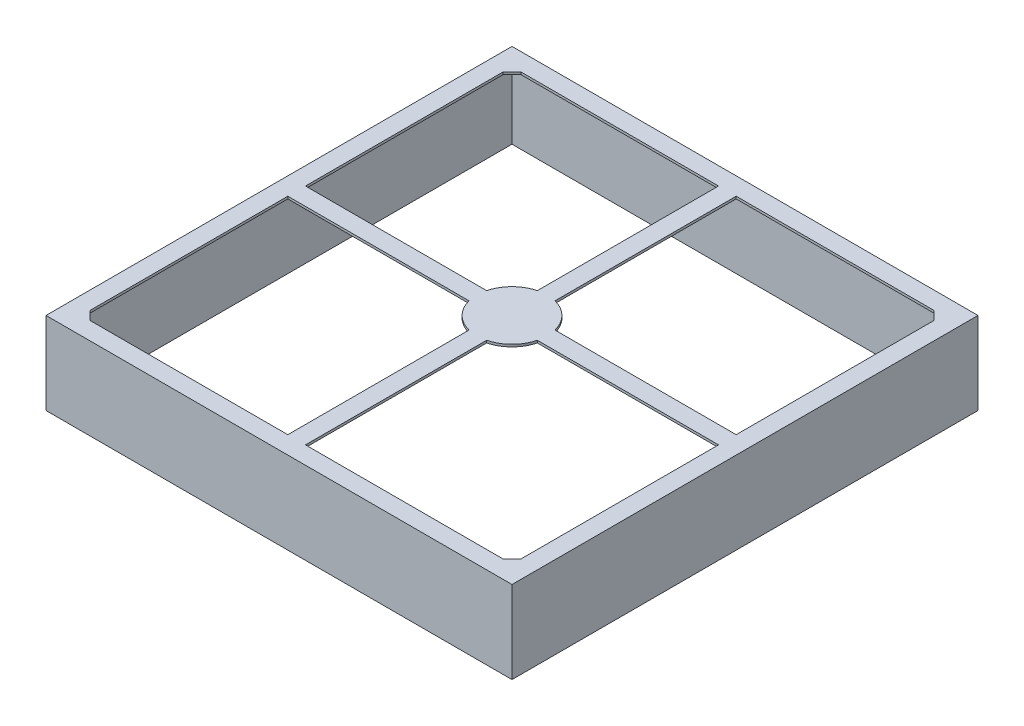
SolidWorks part; units mm, degrees
material "Magnesium Alloy"
ref_plane "Front Plane" through (0, 0, 0) normal (0, 0, 1) x (1, 0, 0)
ref_plane "Top Plane" through (0, 0, 0) normal (0, 1, 0) x (1, 0, 0)
ref_plane "Right Plane" through (0, 0, 0) normal (1, 0, 0) x (0, 0, -1)
sketch "Sketch1" plane through (0, 0, 0) normal (0, 1, 0) x (1, 0, 0)
  line L1 (-19.8, -19.8) -> (19.8, -19.8)
  line L2 (-19.8, -19.8) -> (-19.8, 19.8)
  line L3 (-19.8, 19.8) -> (19.8, 19.8)
  line L4 (19.8, -19.8) -> (19.8, 19.8)
  line L5 (-19.8, -19.8) -> (19.8, 19.8) construction
  line L6 (-19.8, 19.8) -> (19.8, -19.8) construction
  point P0 (0, 0)
  dimension "D1" = 39.6
extrude "Boss-Extrude1" add sketch "Sketch1" along normal blind 7
shell "Shell2" thickness 0.2
sketch "Sketch2" plane through (0, 0, 0) normal (0, 1, 0) x (1, 0, 0)
  line L0 (19.8, 19.8) -> (-19.8, 19.8) construction
  line L1 (17.55, -18.3) -> (0.75, -18.3)
  line L2 (18.3, -17.55) -> (18.3, -0.75)
  line L3 (17.55, 18.3) -> (0.75, 18.3)
  line L4 (-18.3, -17.55) -> (-18.3, -0.75)
  line L5 (18.3, -18.3) -> (-18.3, 18.3) construction
  line L6 (18.3, 18.3) -> (-18.3, -18.3) construction
  line L7 (0, 19.8) -> (0, -18.3) construction
  line L8 (19.8, 0) -> (-19.8, 0) construction
  line L9 (-0.75, 18.3) -> (-0.75, 2.9047)
  line L10 (18.3, 0.75) -> (2.9047, 0.75)
  line L11 (0.75, 18.3) -> (0.75, 2.9047)
  line L12 (18.3, -0.75) -> (2.9047, -0.75)
  line L13 (-2.9047, -0.75) -> (-18.3, -0.75)
  line L14 (18.3, -0.75) -> (-18.3, -0.75) construction
  line L15 (-2.9047, 0.75) -> (-18.3, 0.75)
  line L16 (18.3, 0.75) -> (-18.3, 0.75) construction
  line L17 (-0.75, -2.9047) -> (-0.75, -18.3)
  line L18 (-0.75, 18.3) -> (-0.75, -18.3) construction
  line L19 (0.75, -2.9047) -> (0.75, -18.3)
  line L20 (0.75, 18.3) -> (0.75, -18.3) construction
  line L21 (-18.3, 0.75) -> (-18.3, 17.55)
  line L22 (-0.75, -18.3) -> (-17.55, -18.3)
  line L23 (18.3, 0.75) -> (18.3, 17.55)
  line L24 (-0.75, 18.3) -> (-17.55, 18.3)
  line L25 (-19.8, 19.8) -> (-19.8, -19.8) construction
  line L26 (18.3, 0) -> (-18.3, 0) construction
  line L27 (-17.55, 18.3) -> (-18.3, 17.55)
  line L28 (18.3, 17.55) -> (17.55, 18.3)
  line L29 (19.8, -19.8) -> (19.8, 19.8) construction
  line L30 (0, 18.3) -> (0, -18.3) construction
  line L31 (17.55, -18.3) -> (18.3, -17.55)
  line L32 (-17.55, -18.3) -> (-18.3, -17.55)
  arc A0 (-2.9047, -0.75) -> (-0.75, -2.9047) centre (0, 0) ccw
  arc A1 (0.75, -2.9047) -> (2.9047, -0.75) centre (0, 0) ccw
  arc A2 (2.9047, 0.75) -> (0.75, 2.9047) centre (0, 0) ccw
  arc A3 (-0.75, 2.9047) -> (-2.9047, 0.75) centre (0, 0) ccw
  point P0 (0, 0)
  dimension "D2" = 6
  dimension "D1" = 1.5
  dimension "D5" = 1.5
  dimension "D3" = 0.75
  dimension "D4" = 0.75
extrude "Cut-Extrude1" cut sketch "Sketch2" along normal through all
